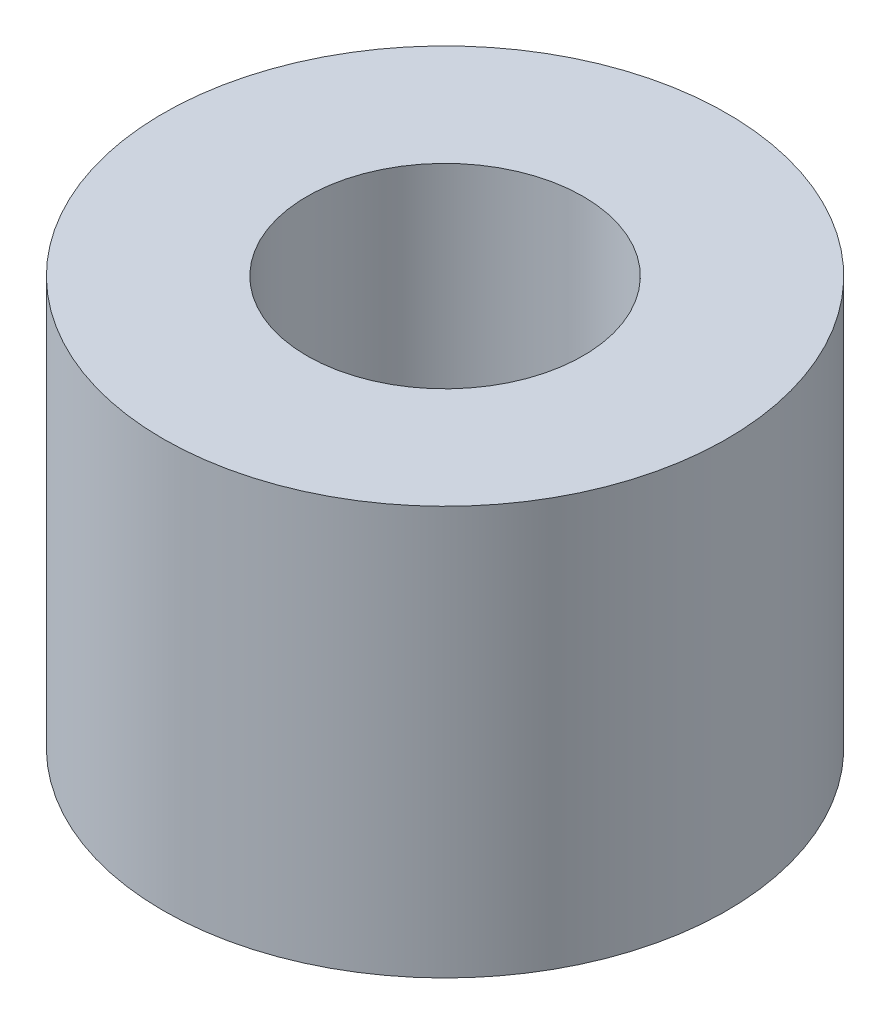
SolidWorks part; units mm, degrees
ref_plane "Front Plane" through (0, 0, 0) normal (0, 0, 1) x (1, 0, 0)
ref_plane "Top Plane" through (0, 0, 0) normal (0, 1, 0) x (1, 0, 0)
ref_plane "Right Plane" through (0, 0, 0) normal (1, 0, 0) x (0, 0, -1)
sketch "Sketch1" plane through (0, 0, 0) normal (0, 1, 0) x (1, 0, 0)
  circle A0 centre (0, 0) radius 2.45
  circle A1 centre (0, 0) radius 1.2
  dimension "D1" = 4.9
  dimension "D2" = 2.4
extrude "Boss-Extrude1" add sketch "Sketch1" along normal blind 3.55
